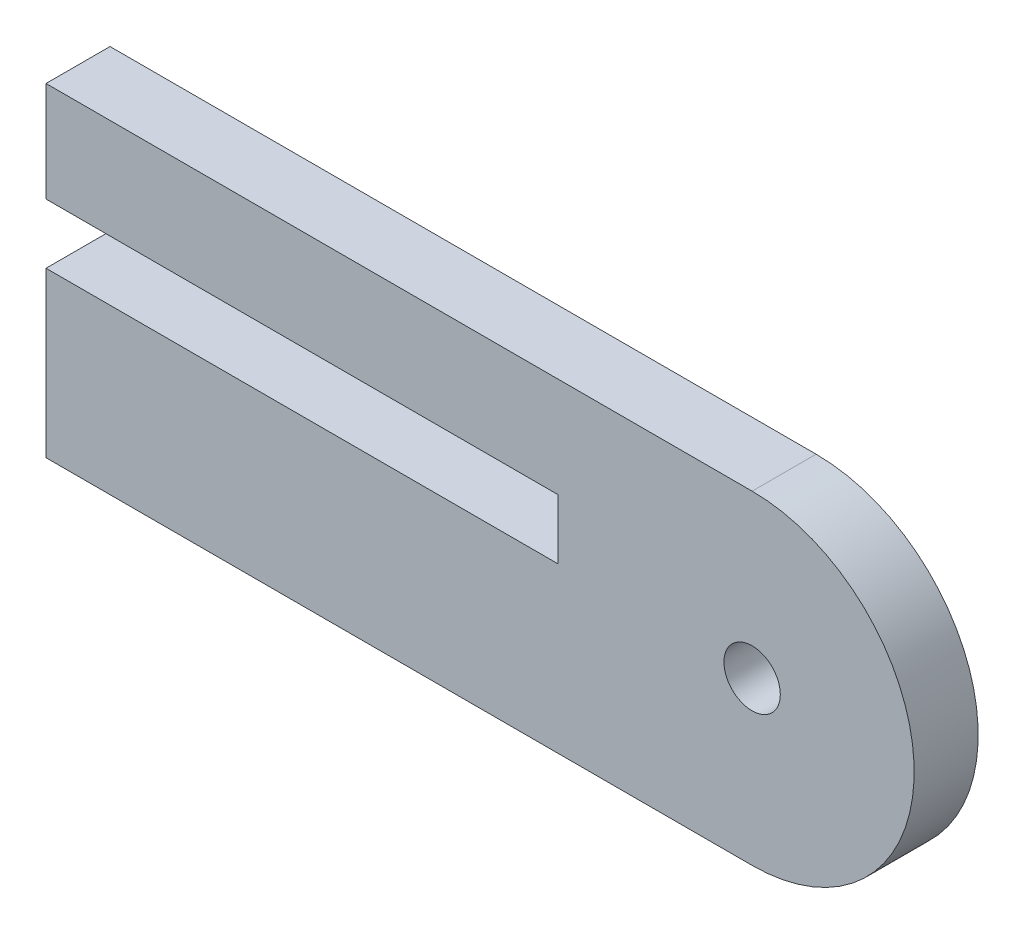
SolidWorks part; units mm, degrees
ref_plane "Front Plane" through (0, 0, 0) normal (0, 0, 1) x (1, 0, 0)
ref_plane "Top Plane" through (0, 0, 0) normal (0, 1, 0) x (1, 0, 0)
ref_plane "Right Plane" through (0, 0, 0) normal (1, 0, 0) x (0, 0, -1)
sketch "Sketch1" plane through (0, 0, 0) normal (0, 0, 1) x (1, 0, 0)
  line L0 (26.9875, 7.9375) -> (42.8625, 7.9375) construction
  line L1 (0, 0) -> (34.925, 0) construction
  line L2 (0, 0) -> (0, 4.7625) construction
  line L3 (0, 15.875) -> (34.925, 15.875) construction
  line L4 (42.8625, 0) -> (42.8625, 7.9375) construction
  line L5 (0, 11.1125) -> (25.4, 11.1125) construction
  line L6 (0, 11.1125) -> (0, 4.7625) construction
  line L7 (0, 4.7625) -> (26.9875, 4.7625) construction
  line L8 (26.9875, 11.1125) -> (26.9875, 4.7625) construction
  line L9 (42.8625, 7.9375) -> (42.8625, 15.875) construction
  line L10 (34.925, 0) -> (42.8625, 0) construction
  line L11 (34.925, 15.875) -> (42.8625, 15.875) construction
  line L12 (0, 4.7625) -> (0, 11.1125) construction
  line L13 (0, 11.1125) -> (0, 15.875) construction
  line L14 (25.4, 11.1125) -> (25.4, 7.9375) construction
  line L15 (0, 4.7625) -> (26.9875, 4.7625) construction
  line L16 (0, 4.7625) -> (0, 7.9375) construction
  line L17 (0, 7.9375) -> (25.4, 7.9375) construction
  line L18 (26.9875, 4.7625) -> (26.9875, 7.9375)
  line L19 (25.4, 11.1125) -> (26.9875, 11.1125) construction
  line L20 (25.4, 7.9375) -> (26.9875, 7.9375) construction
  line L21 (-0.1016, 15.9766) -> (34.925, 15.9766)
  line L22 (-0.1016, -0.1016) -> (34.925, -0.1016)
  line L23 (-0.1016, -0.1016) -> (-0.1016, 4.7625)
  line L24 (-0.1016, 4.7625) -> (-0.1016, 8.0391)
  line L25 (-0.1016, 8.0391) -> (25.2984, 8.0391)
  line L26 (25.2984, 11.0109) -> (25.2984, 8.0391)
  line L27 (-0.1016, 11.0109) -> (25.2984, 11.0109)
  line L28 (-0.1016, 11.0109) -> (-0.1016, 15.9766)
  arc A0 (34.925, 0) -> (34.925, 15.875) centre (34.925, 7.9375) ccw construction
  arc A1 (26.9875, 7.9375) -> (34.925, 0) centre (34.925, 7.9375) ccw construction
  arc A2 (34.925, 15.875) -> (26.9875, 7.9375) centre (34.925, 7.9375) ccw construction
  circle A3 centre (34.925, 7.9375) radius 1.5 construction
  arc A4 (34.925, -0.1016) -> (34.925, 15.9766) centre (34.925, 7.9375) ccw
  circle A5 centre (34.925, 7.9375) radius 1.3984
  point P15 (34.925, 7.9375)
  dimension "D5" = 15.875
  dimension "D6" = 3
  dimension "D1" = 15.875
  dimension "D2" = 6.35
  dimension "D3" = 26.9875
  dimension "D4" = 15.875
  dimension "D7" = 25.4
  dimension "D8" = 0.1016
  dimension "D9" = 0.1016
extrude "Boss-Extrude1" add sketch "Sketch1" along normal blind 3.175 contours L1 A0 L3 L13 L5 L8 L7 L2 A3 | L17 L16 L7 L8 | L21 A4 L22 L23 L24 L25 L26 L27 L28 | A5
